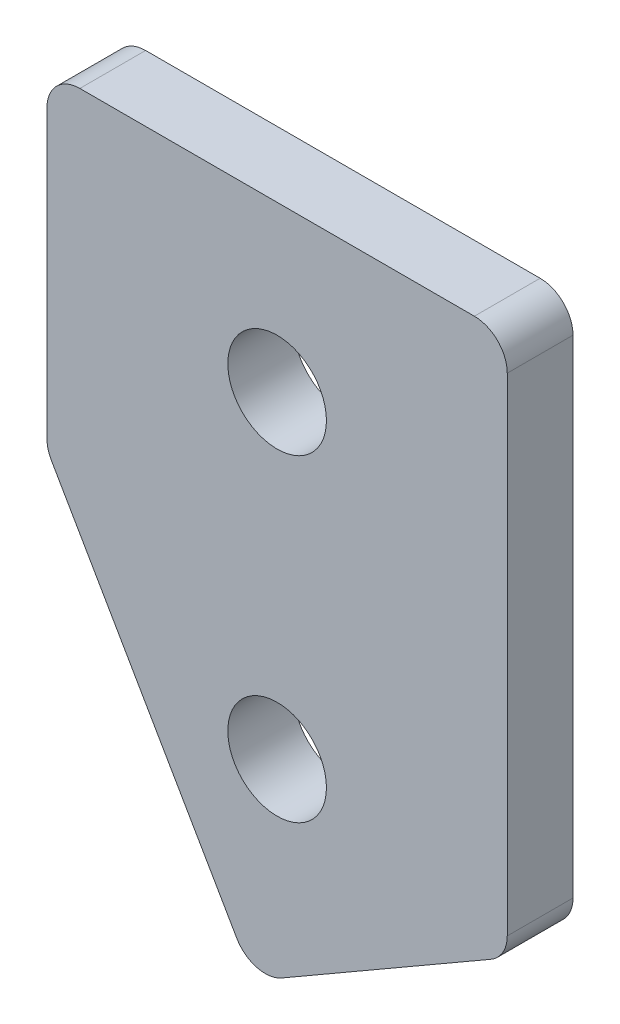
SolidWorks part; units mm, degrees
material "环氧板3240"
ref_plane "前视基准面" through (0, 0, 0) normal (0, 0, 1) x (1, 0, 0)
ref_plane "上视基准面" through (0, 0, 0) normal (0, 1, 0) x (1, 0, 0)
ref_plane "右视基准面" through (0, 0, 0) normal (1, 0, 0) x (0, 0, -1)
other "Configuration Table"
sketch "草图1" plane through (0, 0, 0) normal (0, 0, 1) x (1, 0, 0)
  line L0 (0, 10) -> (14, 10)
  line L1 (14, 10) -> (14, -6.4021)
  line L2 (14, -6.4021) -> (6.2722, -10.8637)
  line L3 (6.2722, -10.8637) -> (0, 0)
  line L4 (0, 0) -> (0, 10)
  line L5 (0, 0) -> (14, 0) construction
  line L6 (0, 5) -> (14, 5) construction
  line L7 (3.7722, -6.5336) -> (7, -4.67) construction
  circle A1 centre (7, 5) radius 1.5
  circle A2 centre (7, -4.67) radius 1.5
  dimension "D4" = 3
  dimension "D7" = 7
  dimension "D6" = 7
  dimension "D2" = 9.67
  dimension "D5" = 0
  dimension "D1" = 10
  dimension "D3" = 5
  dimension "D8" = 30
extrude "凸台-拉伸1" add sketch "草图1" along normal blind 2
fillet "圆角1" radius 1 5 edges at (6.2722, -10.8637, 1) (14, -6.4021, 1) (14, 10, 1) (0, 0, 1) (0, 10, 1)
